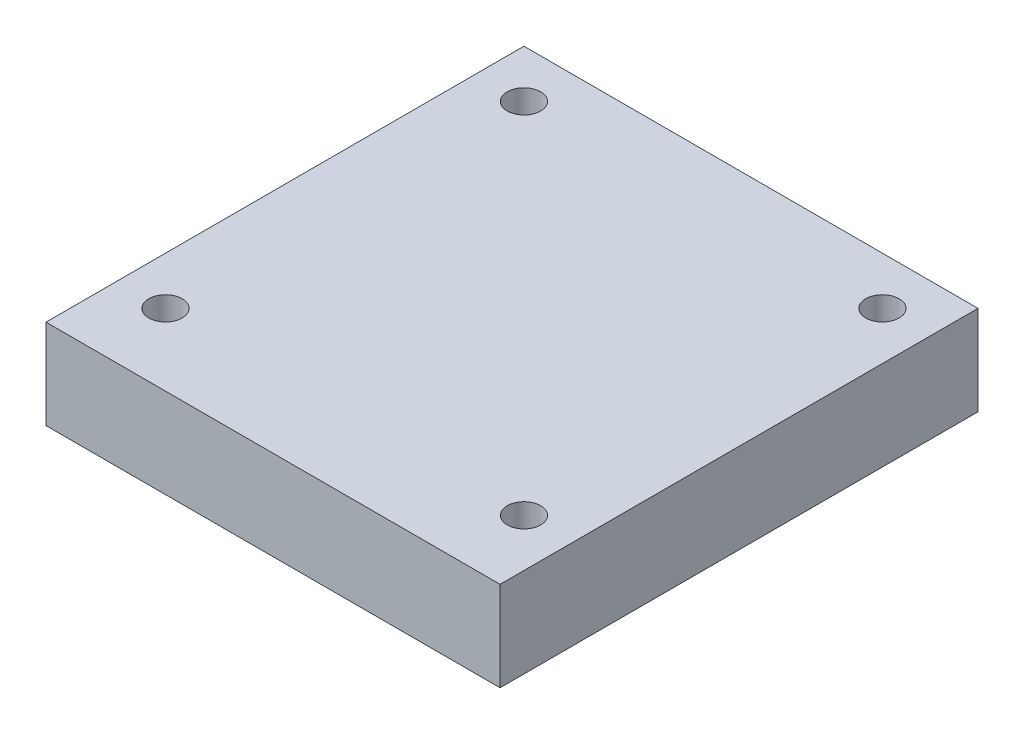
SolidWorks part; units mm, degrees
ref_plane "Front Plane" through (0, 0, 0) normal (0, 0, 1) x (1, 0, 0)
ref_plane "Top Plane" through (0, 0, 0) normal (0, 1, 0) x (1, 0, 0)
ref_plane "Right Plane" through (0, 0, 0) normal (1, 0, 0) x (0, 0, -1)
sketch "Sketch1" plane through (0, 0, 0) normal (0, 1, 0) x (1, 0, 0)
  line L1 (0, 0) -> (38, 0)
  line L2 (0, 0) -> (0, 40)
  line L3 (0, 40) -> (38, 40)
  line L4 (38, 0) -> (38, 40)
  circle A0 centre (4, 36) radius 1.3979
  circle A1 centre (34, 36) radius 1.3979
  circle A2 centre (4, 6) radius 1.3979
  circle A3 centre (34, 6) radius 1.3979
  dimension "D1" = 30
  dimension "D2" = 38
  dimension "D3" = 4
  dimension "D4" = 4
  dimension "D5" = 30
extrude "Boss-Extrude1" add sketch "Sketch1" along normal blind 7.5
